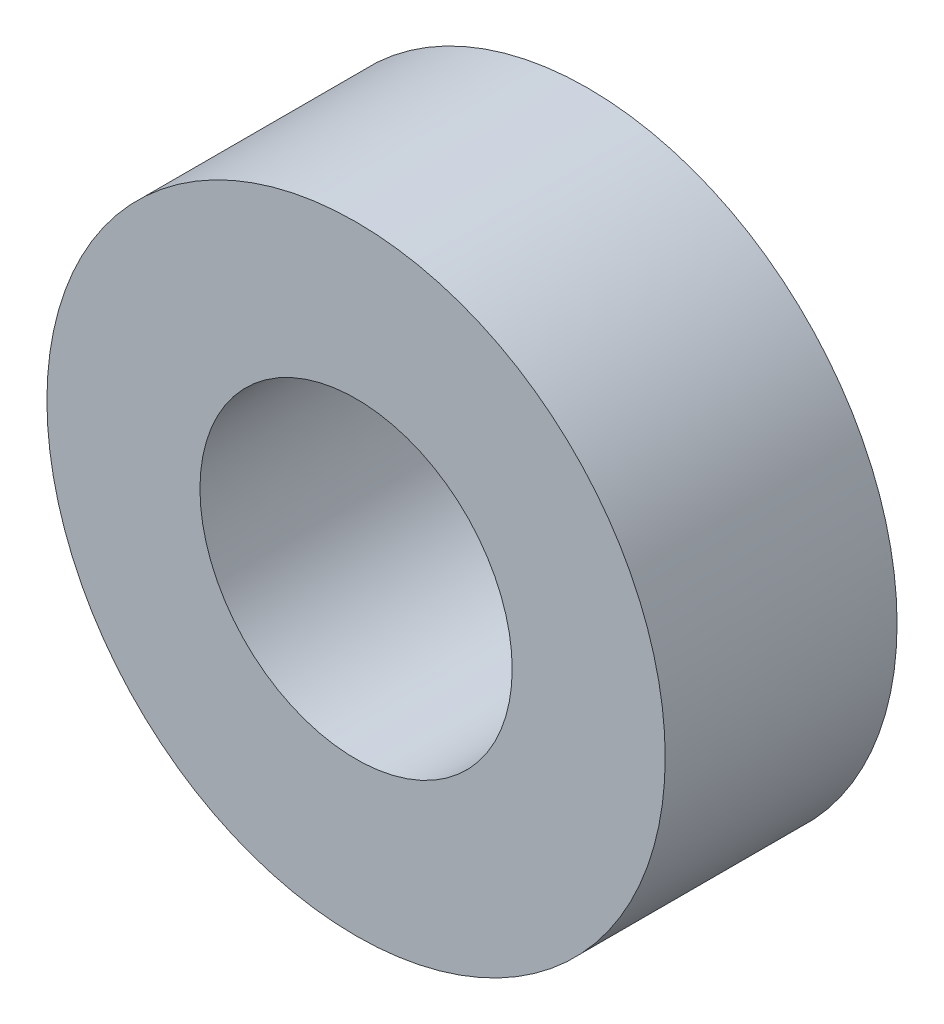
SolidWorks part; units mm, degrees
material "Nylon 6/10"
ref_plane "Front" through (0, 0, 0) normal (0, 0, 1) x (1, 0, 0)
ref_plane "Top" through (0, 0, 0) normal (0, 1, 0) x (1, 0, 0)
ref_plane "Right" through (0, 0, 0) normal (1, 0, 0) x (0, 0, -1)
sketch "Sketch1" plane through (0, 0, 0) normal (0, 0, 1) x (1, 0, 0)
  circle A0 centre (0, 0) radius 6.4135
  circle A1 centre (0, 0) radius 12.7
  dimension "D1" = 12.827
extrude "Boss-Extrude1" add sketch "Sketch1" along normal blind 9.525
